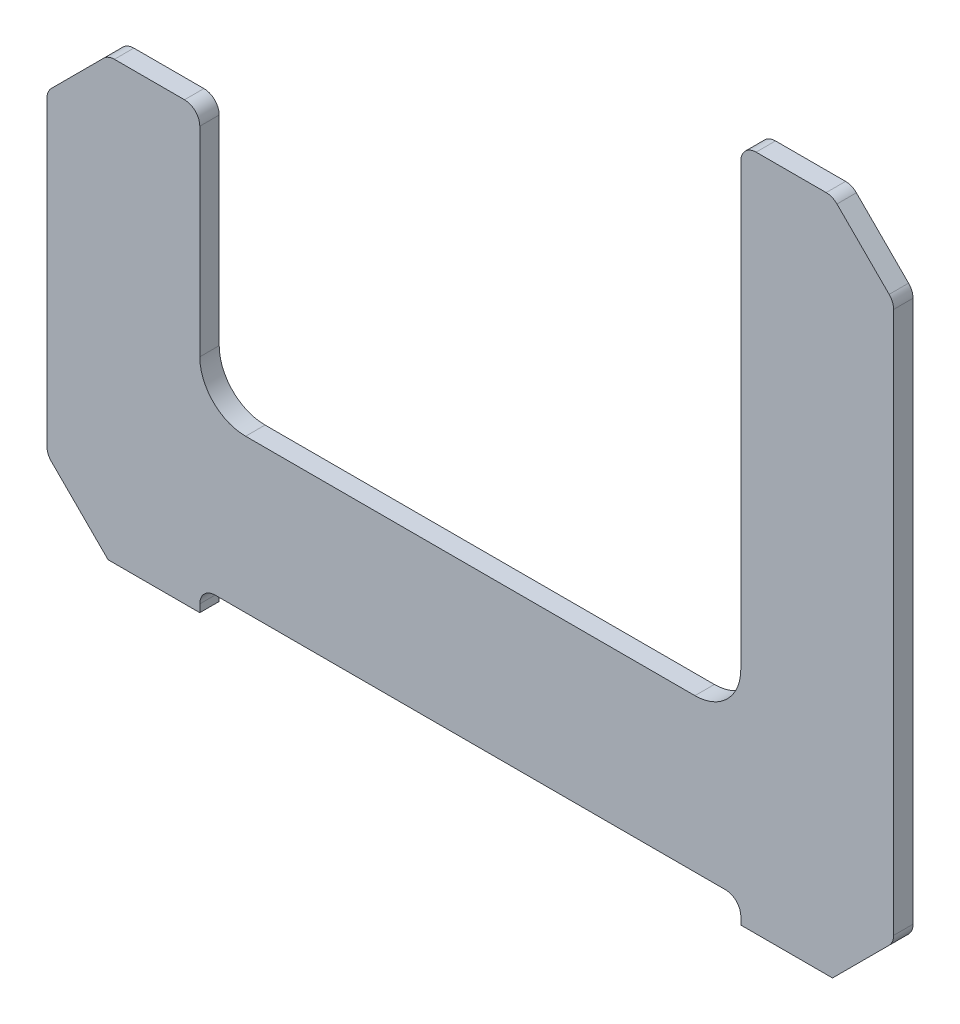
SolidWorks part; units mm, degrees
material "Cedar"
ref_plane "Front Plane" through (0, 0, 0) normal (0, 0, 1) x (1, 0, 0)
ref_plane "Top Plane" through (0, 0, 0) normal (0, 1, 0) x (1, 0, 0)
ref_plane "Right Plane" through (0, 0, 0) normal (1, 0, 0) x (0, 0, -1)
sketch "Sketch2" plane through (0, 0, 0) normal (0, 0, 1) x (1, 0, 0)
  line L0 (-138.5, 85.3385) -> (-88.5, 85.3385)
  line L1 (-88.5, 85.3385) -> (-88.5, 0)
  line L2 (-88.5, 0) -> (88.5, 0)
  line L3 (88.5, 0) -> (88.5, 164)
  line L4 (88.5, 164) -> (138.5, 164)
  line L5 (138.5, 164) -> (138.5, -57.5)
  line L6 (138.5, -57.5) -> (88.5, -57.5)
  line L7 (88.5, -57.5) -> (88.5, -50)
  line L8 (88.5, -50) -> (-88.5, -50)
  line L9 (-88.5, -50) -> (-88.5, -57.5)
  line L10 (-88.5, -57.5) -> (-138.5, -57.5)
  line L11 (-138.5, -57.5) -> (-138.5, 85.3385)
  line L12 (-33.5, 0) -> (-33.5, 124) construction
  point P10 (-33.5, 0)
  point P14 (88.5, 124)
  point P15 (-33.5, 85.3385)
  dimension "D1" = 124
  dimension "D2" = 122
  dimension "D3" = 55
  dimension "D4" = 40
  dimension "D5" = 50
  dimension "D6" = 50
  dimension "D7" = 7.5
extrude "Boss-Extrude1" add sketch "Sketch2" along normal blind 3.175 and the other way blind 3.175
chamfer "Chamfer1" distance 20 angle 45 4 edges at (-138.5, -57.5, 0) (138.5, -57.5, 0) (138.5, 164, 0) (-138.5, 85.3385, 0)
fillet "Fillet1" radius 15 2 edges at (88.5, 0, 0) (-88.5, 0, 0)
fillet "Fillet2" radius 5 10 edges at (138.5, -37.5, 0) (88.5, -50, 0) (-88.5, -50, 0) (-138.5, -37.5, 0) (-138.5, 65.3385, 0) (-118.5, 85.3385, 0) (-88.5, 85.3385, 0) (138.5, 144, 0) (118.5, 164, 0) (88.5, 164, 0)
sketch "Sketch3" plane through (0, 0, 3.175) normal (0, 0, 1) x (1, 0, 0)
  line L0 (-94.6381, 69.9757) -> (-94.6381, 14.7992)
  line L1 (-94.6381, 14.7992) -> (-97.8131, 14.7992)
  line L2 (-97.8131, 14.7992) -> (-97.8131, 69.9757)
  line L3 (-97.8131, 69.9757) -> (-94.6381, 69.9757)
  line L4 (-127.4635, 65.4691) -> (-114.3536, 78.579)
  line L5 (-114.3536, 78.579) -> (-112.1085, 76.3339)
  line L6 (-112.1085, 76.3339) -> (-125.2184, 63.2241)
  line L7 (-125.2184, 63.2241) -> (-127.4635, 65.4691)
  line L8 (-129.3392, 54.7846) -> (-126.1642, 54.7846)
  line L9 (-126.1642, 54.7846) -> (-126.1642, -28.3138)
  line L10 (-126.1642, -28.3138) -> (-129.3392, -28.3138)
  line L11 (-129.3392, -28.3138) -> (-129.3392, 54.7846)
  line L12 (-127.4635, -37.1329) -> (-125.2184, -34.8879)
  line L13 (-125.2184, -34.8879) -> (-110.9382, -49.1681)
  line L14 (-110.9382, -49.1681) -> (-113.1832, -51.4132)
  line L15 (-113.1832, -51.4132) -> (-127.4635, -37.1329)
  line L16 (-67.7784, -44.3183) -> (-67.7784, -41.1433)
  line L17 (-67.7784, -41.1433) -> (53.0181, -41.1433)
  line L18 (53.0181, -41.1433) -> (53.0181, -44.3183)
  line L19 (53.0181, -44.3183) -> (-67.7784, -44.3183)
  line L20 (114.9313, -49.5303) -> (117.1763, -51.7753)
  line L21 (117.1763, -51.7753) -> (131.7883, -37.1634)
  line L22 (131.7883, -37.1634) -> (129.5432, -34.9183)
  line L23 (129.5432, -34.9183) -> (114.9313, -49.5303)
  line L24 (-67.7784, -4.1746) -> (-67.7784, -7.3496)
  line L25 (-67.7784, -7.3496) -> (63.5847, -7.3496)
  line L26 (63.5847, -7.3496) -> (63.5847, -4.1746)
  line L27 (63.5847, -4.1746) -> (-67.7784, -4.1746)
  line L28 (92.7516, 20.9162) -> (91.2159, 151.9937)
  line L29 (91.2159, 151.9937) -> (94.3909, 151.9937)
  line L30 (94.3909, 151.9937) -> (95.9266, 20.9162)
  line L31 (95.9266, 20.9162) -> (92.7516, 20.9162)
  line L32 (96.8341, 161.8762) -> (96.8341, 158.7012)
  line L33 (96.8341, 158.7012) -> (112.5649, 158.7012)
  line L34 (112.5649, 158.7012) -> (112.5649, 161.8762)
  line L35 (112.5649, 161.8762) -> (96.8341, 161.8762)
  line L37 (117.7781, 156.4535) -> (120.0231, 158.6985)
  line L38 (120.0231, 158.6985) -> (133.8694, 144.8523)
  line L39 (133.8694, 144.8523) -> (131.6243, 142.6072)
  line L40 (131.6243, 142.6072) -> (117.7781, 156.4535)
  line L41 (129.9213, 134.1701) -> (133.0963, 134.1701)
  line L42 (133.0963, 134.1701) -> (133.0963, -24.961)
  line L43 (133.0963, -24.961) -> (129.9213, -24.961)
  line L44 (129.9213, -24.961) -> (129.9213, 134.1701)
  line L45 (118.5, -57.5) -> (137.0355, -38.9645) construction
  line L46 (-137.0355, -38.9645) -> (-118.5, -57.5) construction
  line L47 (-119.9645, 83.874) -> (-137.0355, 66.8029) construction
  line L48 (137.0355, 145.4645) -> (119.9645, 162.5355) construction
  dimension "D1" = 3.175
extrude "Cut-Extrude1" [suppressed] cut sketch "Sketch3" against normal through all
sketch "magnets" plane through (0, 0, 3.175) normal (0, 0, 1) x (1, 0, 0)
  point P0 (94.6751, 158.4052)
  point P1 (114.7572, -50)
  point P2 (131.9288, 140.6094)
  point P3 (131.9288, -32.8111)
  point P4 (0, -44.1618)
  point P5 (-114.0039, -50)
  point P6 (-130.8821, -32.8111)
  point P9 (-130.8821, 62.3605)
  point P10 (-93.5499, 79.7316)
  point P12 (0, -4.7392)
sketch "Sketch4" plane through (0, 0, 3.175) normal (0, 0, 1) x (1, 0, 0)
  line L0 (99.9645, 164) -> (99.9645, 160.825)
  line L1 (116.4289, 164) -> (93.5, 164) construction
  line L2 (99.9645, 160.825) -> (109.9645, 160.825)
  line L3 (109.9645, 160.825) -> (109.9645, 164)
  line L4 (124.9645, 157.5355) -> (122.7194, 155.2905)
  line L5 (137.0355, 145.4645) -> (119.9645, 162.5355) construction
  line L6 (122.7194, 155.2905) -> (129.7905, 148.2194)
  line L7 (129.7905, 148.2194) -> (132.0355, 150.4645)
  line L8 (88.5, 137) -> (91.675, 137)
  line L9 (88.5, 159) -> (88.5, 15) construction
  line L10 (91.675, 137) -> (91.675, 37)
  line L11 (91.675, 37) -> (88.5, 37)
  line L12 (138.5, 103.25) -> (135.325, 103.25)
  line L13 (138.5, -35.4289) -> (138.5, 141.9289) construction
  line L14 (135.325, 103.25) -> (135.325, 3.25)
  line L15 (135.325, 3.25) -> (138.5, 3.25)
  line L16 (-50, 0) -> (-50, -3.175)
  line L17 (73.5, 0) -> (-73.5, 0) construction
  line L18 (-50, -3.175) -> (50, -3.175)
  line L19 (50, -3.175) -> (50, 0)
  line L20 (-50, -50) -> (-50, -46.825)
  line L21 (-83.5, -50) -> (83.5, -50) construction
  line L22 (-50, -46.825) -> (50, -46.825)
  line L23 (50, -46.825) -> (50, -50)
  line L24 (-135.325, -6.0808) -> (-138.5, -6.0808)
  line L25 (-138.5, 63.2674) -> (-138.5, -35.4289) construction
  line L26 (-135.325, 33.9192) -> (-135.325, -6.0808)
  line L27 (-135.325, 33.9192) -> (-138.5, 33.9192)
  line L28 (-132.0355, 71.8029) -> (-129.7905, 69.5579)
  line L29 (-119.9645, 83.874) -> (-137.0355, 66.8029) construction
  line L30 (-129.7905, 69.5579) -> (-122.7194, 76.6289)
  line L31 (-122.7194, 76.6289) -> (-124.9645, 78.874)
  line L32 (-109.9645, 85.3385) -> (-109.9645, 82.1635)
  line L33 (-93.5, 85.3385) -> (-116.4289, 85.3385) construction
  line L35 (-109.9645, 82.1635) -> (-99.9645, 82.1635)
  line L36 (-88.5, 67.6692) -> (-91.675, 67.6692)
  line L37 (-88.5, 15) -> (-88.5, 80.3385) construction
  line L38 (-91.675, 67.6692) -> (-91.675, 27.6692)
  line L39 (-91.675, 27.6692) -> (-88.5, 27.6692)
  line L40 (-107.375, -57.5) -> (-107.375, -54.325)
  line L41 (-118.5, -57.5) -> (-88.5, -57.5) construction
  line L42 (-107.375, -54.325) -> (-97.375, -54.325)
  line L43 (-97.375, -54.325) -> (-97.375, -57.5)
  line L44 (97.375, -57.5) -> (97.375, -54.325)
  line L45 (88.5, -57.5) -> (118.5, -57.5) construction
  line L46 (97.375, -54.325) -> (107.375, -54.325)
  line L47 (107.375, -54.325) -> (107.375, -57.5)
  line L48 (-132.0988, -43.9012) -> (-129.8537, -41.6561)
  line L49 (-137.0355, -38.9645) -> (-118.5, -57.5) construction
  line L50 (-129.8537, -41.6561) -> (-122.7827, -48.7272)
  line L51 (-122.7827, -48.7272) -> (-125.0277, -50.9723)
  line L52 (125.0277, -50.9723) -> (122.7827, -48.7272)
  line L53 (118.5, -57.5) -> (137.0355, -38.9645) construction
  line L54 (122.7827, -48.7272) -> (129.8537, -41.6561)
  line L55 (129.8537, -41.6561) -> (132.0988, -43.9012)
  line L56 (-128.5633, -47.4367) -> (-126.3182, -45.1917) construction
  line L57 (-102.375, -57.5) -> (-102.375, -54.325)
  line L58 (102.375, -57.5) -> (102.375, -54.325)
  line L59 (-128.5, 75.3385) -> (-126.2549, 73.0934) construction
  line L60 (-104.9645, 82.1635) -> (-104.9645, 85.3385) construction
  line L61 (126.2549, 151.7549) -> (128.5, 154) construction
  line L62 (126.3182, -45.1917) -> (128.5633, -47.4367) construction
  line L63 (88.5, -57.5) -> (116.25, -57.5) construction
  line L64 (120.091, -55.909) -> (137.0355, -38.9645) construction
  line L65 (120.091, -55.909) -> (118.5, -57.5) construction
  line L66 (118.5, -57.5) -> (116.25, -57.5) construction
  line L67 (-88.5, -57.5) -> (-116.25, -57.5) construction
  line L68 (-116.25, -57.5) -> (-118.5, -57.5) construction
  line L69 (-118.5, -57.5) -> (-120.091, -55.909) construction
  line L70 (-120.091, -55.909) -> (-137.0355, -38.9645) construction
  line L71 (-99.9645, 82.1635) -> (-99.9645, 85.3385)
  point P95 (0, -46.825)
  point P97 (0, -50)
  point P99 (0, -3.175)
  point P101 (135.325, 53.25)
  point P103 (138.5, 53.25)
  point P104 (91.675, 87)
  point P105 (88.5, 87)
  point P106 (104.9645, 160.825)
  point P107 (104.9645, 164)
  point P108 (128.5, 154)
  point P109 (126.2549, 151.7549)
  point P112 (-135.325, 13.9192)
  point P113 (-138.5, 13.9192)
  point P114 (-91.675, 47.6692)
  point P115 (-88.5, 47.6692)
  point P116 (126.3182, -45.1917)
  point P117 (127.7678, -48.2322)
  line M1 (118.5, -57.5) -> (137.0355, -38.9645)
  line M3 (138.5, -35.4289) -> (138.5, 141.9289)
  line M5 (137.0355, 145.4645) -> (119.9645, 162.5355)
  line M7 (116.4289, 164) -> (93.5, 164)
  line M9 (88.5, 159) -> (88.5, 15)
  line M11 (73.5, 0) -> (-73.5, 0)
  line M13 (-88.5, 15) -> (-88.5, 80.3385)
  line M15 (-93.5, 85.3385) -> (-116.4289, 85.3385)
  line M17 (-119.9645, 83.874) -> (-137.0355, 66.8029)
  line M19 (-138.5, 63.2674) -> (-138.5, -35.4289)
  line M21 (-137.0355, -38.9645) -> (-118.5, -57.5)
  line M22 (-118.5, -57.5) -> (-88.5, -57.5)
  line M25 (-83.5, -50) -> (83.5, -50)
  line M28 (88.5, -57.5) -> (118.5, -57.5)
  dimension "D1" = 3.175
  dimension "D5" = 100
  dimension "D6" = 100
  dimension "D7" = 100
  dimension "D8" = 100
  dimension "D4" = 10
  dimension "D2" = 10
  dimension "D10" = 2.25
  dimension "D3" = 2.25
  dimension "D11" = 10
  dimension "D13" = 3.175
  dimension "D12" = 10
  dimension "D14" = 10
  dimension "D15" = 10
  dimension "D16" = 10
  dimension "D17" = 10
  dimension "D18" = 40
  dimension "D19" = 3.175
extrude "wall_slots" [suppressed] cut sketch "Sketch4" against normal blind 60 contours L26 L27 L24 M19 | L18 L19 L16 M11 | L23 L22 L20 M25 | L51 L50 L48 M21 | L57 L43 L42 M22 | L57 L42 L40 M22 | L38 L39 L36 M13 | L35 L71 L32 M15 | L30 L31 L28 M17 | L58 L47 L46 M28 | L58 L46 L44 M28 | L55 L54 L52 M1 | L14 L15 L12 M3 | L11 L10 L8 M9 | L2 L3 L0 M7 | L6 L7 L4 M5
sketch "wall_measure" [suppressed] plane through (0, 0, 3.175) normal (0, 0, 1) x (1, 0, 0)
  line L0 (-116.4289, 85.3385) -> (-116.4289, 82.1635)
  line L1 (-116.4289, 82.1635) -> (-93.5, 82.1635)
  line L2 (-93.5, 82.1635) -> (-93.5, 85.3385)
  line L4 (93.5, 164) -> (93.5, 160.825)
  line L5 (93.5, 160.825) -> (116.4289, 160.825)
  line L6 (116.4289, 160.825) -> (116.4289, 164)
  line L7 (99.9645, 160.825) -> (109.9645, 160.825) construction
  line L8 (119.9645, 162.5355) -> (117.7194, 160.2905)
  line L9 (117.7194, 160.2905) -> (134.7905, 143.2194)
  line L10 (134.7905, 143.2194) -> (137.0355, 145.4645)
  line L11 (137.0355, 145.4645) -> (132.0355, 150.4645) construction
  line L12 (88.5, 159) -> (91.675, 159)
  line L13 (91.675, 159) -> (91.675, 15)
  line L14 (91.675, 15) -> (88.5, 15)
  line L15 (88.5, 37) -> (88.5, 15) construction
  line L16 (138.5, 141.9289) -> (135.325, 141.9289)
  line L17 (135.325, 141.9289) -> (135.325, -35.4289)
  line L18 (135.325, -35.4289) -> (138.5, -35.4289)
  line L19 (-73.5, 0) -> (-73.5, -3.175)
  line L20 (-73.5, -3.175) -> (73.5, -3.175)
  line L21 (73.5, -3.175) -> (73.5, 0)
  line L22 (-83.5, -50) -> (-83.5, -46.825)
  line L23 (-83.5, -46.825) -> (83.5, -46.825)
  line L24 (83.5, -46.825) -> (83.5, -50)
  line L25 (88.5, -55) -> (116.2868, -55)
  line L26 (116.2868, -55) -> (116.2868, -57.5)
  line L27 (137.0355, -38.9645) -> (134.7905, -36.7194)
  line L28 (134.7905, -36.7194) -> (117.8199, -53.69)
  line L29 (117.8199, -53.69) -> (120.065, -55.935)
  line L30 (118.5, -57.5) -> (125.0277, -50.9723) construction
  line L31 (122.7827, -48.7272) -> (129.8537, -41.6561) construction
  line L32 (116.2868, -57.5) -> (118.5, -57.5) construction
  line L33 (118.5, -57.5) -> (120.065, -55.935) construction
  line L34 (-138.5, 63.2674) -> (-133.5, 63.2674)
  line L35 (-133.5, 63.2674) -> (-133.5, -35.4289)
  line L36 (-133.5, -35.4289) -> (-138.5, -35.4289)
  line L37 (-88.5, 80.3385) -> (-91.675, 80.3385)
  line L38 (-91.675, 80.3385) -> (-91.675, 15)
  line L39 (-91.675, 15) -> (-88.5, 15)
  line L40 (-50, -46.825) -> (50, -46.825) construction
  line L41 (-50, -3.175) -> (50, -3.175) construction
  line L42 (135.325, 103.25) -> (135.325, 3.25) construction
  line L43 (91.675, 137) -> (91.675, 37) construction
  line L44 (122.7194, 155.2905) -> (129.7905, 148.2194) construction
  line L45 (-91.675, 67.6692) -> (-91.675, 27.6692) construction
  line L47 (-109.9645, 82.1635) -> (-99.9645, 82.1635) construction
  arc A0 (73.5, 0) -> (88.5, 15) centre (73.5, 15) ccw construction
  arc A1 (-88.5, 15) -> (-73.5, 0) centre (-73.5, 15) ccw construction
  dimension "D1" = 22.9289
  dimension "D2" = 22.9289
  dimension "D3" = 24.1421
  dimension "D4" = 144
  dimension "D5" = 177.3579
  dimension "D6" = 147
  dimension "D7" = 167
  dimension "D8" = 24
  dimension "D9" = 2.2132
  dimension "D10" = 27.7868
  dimension "D11" = 98.6963
  dimension "D12" = 65.3385
sketch "perimeter" plane through (0, 0, 3.175) normal (0, 0, 1) x (1, 0, 0)
  line L16 (118.5, -57.5) -> (137.0355, -38.9645)
  line L17 (138.5, -35.4289) -> (138.5, 141.9289)
  line L18 (137.0355, 145.4645) -> (119.9645, 162.5355)
  line L19 (116.4289, 164) -> (93.5, 164)
  line L20 (88.5, 159) -> (88.5, 15)
  line L21 (73.5, 0) -> (-73.5, 0)
  line L22 (-88.5, 15) -> (-88.5, 80.3385)
  line L23 (-93.5, 85.3385) -> (-116.4289, 85.3385)
  line L24 (-119.9645, 83.874) -> (-137.0355, 66.8029)
  line L25 (-138.5, 63.2674) -> (-138.5, -35.4289)
  line L26 (-137.0355, -38.9645) -> (-118.5, -57.5)
  line L27 (-118.5, -57.5) -> (-88.5, -57.5)
  line L28 (-88.5, -57.5) -> (-88.5, -55)
  line L29 (-83.5, -50) -> (83.5, -50)
  line L30 (88.5, -55) -> (88.5, -57.5)
  line L31 (88.5, -57.5) -> (118.5, -57.5)
  line L32 (118.5, -57.5) -> (137.0355, -38.9645)
  line L33 (138.5, -35.4289) -> (138.5, 141.9289)
  line L34 (137.0355, 145.4645) -> (119.9645, 162.5355)
  line L35 (116.4289, 164) -> (93.5, 164)
  line L36 (88.5, 159) -> (88.5, 15)
  line L37 (73.5, 0) -> (-73.5, 0)
  line L38 (-88.5, 15) -> (-88.5, 80.3385)
  line L39 (-93.5, 85.3385) -> (-116.4289, 85.3385)
  line L40 (-119.9645, 83.874) -> (-137.0355, 66.8029)
  line L41 (-138.5, 63.2674) -> (-138.5, -35.4289)
  line L42 (-137.0355, -38.9645) -> (-118.5, -57.5)
  line L43 (-118.5, -57.5) -> (-88.5, -57.5)
  line L44 (-88.5, -57.5) -> (-88.5, -55)
  line L45 (-83.5, -50) -> (83.5, -50)
  line L46 (88.5, -55) -> (88.5, -57.5)
  line L47 (88.5, -57.5) -> (118.5, -57.5)
  arc A12 (137.0355, -38.9645) -> (138.5, -35.4289) centre (133.5, -35.4289) ccw
  arc A13 (138.5, 141.9289) -> (137.0355, 145.4645) centre (133.5, 141.9289) ccw
  arc A14 (119.9645, 162.5355) -> (116.4289, 164) centre (116.4289, 159) ccw
  arc A15 (93.5, 164) -> (88.5, 159) centre (93.5, 159) ccw
  arc A16 (73.5, 0) -> (88.5, 15) centre (73.5, 15) ccw
  arc A17 (-88.5, 15) -> (-73.5, 0) centre (-73.5, 15) ccw
  arc A18 (-88.5, 80.3385) -> (-93.5, 85.3385) centre (-93.5, 80.3385) ccw
  arc A19 (-116.4289, 85.3385) -> (-119.9645, 83.874) centre (-116.4289, 80.3385) ccw
  arc A20 (-137.0355, 66.8029) -> (-138.5, 63.2674) centre (-133.5, 63.2674) ccw
  arc A21 (-138.5, -35.4289) -> (-137.0355, -38.9645) centre (-133.5, -35.4289) ccw
  arc A22 (-83.5, -50) -> (-88.5, -55) centre (-83.5, -55) ccw
  arc A23 (88.5, -55) -> (83.5, -50) centre (83.5, -55) ccw
  arc A24 (137.0355, -38.9645) -> (138.5, -35.4289) centre (133.5, -35.4289) ccw
  arc A25 (138.5, 141.9289) -> (137.0355, 145.4645) centre (133.5, 141.9289) ccw
  arc A26 (119.9645, 162.5355) -> (116.4289, 164) centre (116.4289, 159) ccw
  arc A27 (93.5, 164) -> (88.5, 159) centre (93.5, 159) ccw
  arc A28 (73.5, 0) -> (88.5, 15) centre (73.5, 15) ccw
  arc A29 (-88.5, 15) -> (-73.5, 0) centre (-73.5, 15) ccw
  arc A30 (-88.5, 80.3385) -> (-93.5, 85.3385) centre (-93.5, 80.3385) ccw
  arc A31 (-116.4289, 85.3385) -> (-119.9645, 83.874) centre (-116.4289, 80.3385) ccw
  arc A32 (-137.0355, 66.8029) -> (-138.5, 63.2674) centre (-133.5, 63.2674) ccw
  arc A33 (-138.5, -35.4289) -> (-137.0355, -38.9645) centre (-133.5, -35.4289) ccw
  arc A34 (-83.5, -50) -> (-88.5, -55) centre (-83.5, -55) ccw
  arc A35 (88.5, -55) -> (83.5, -50) centre (83.5, -55) ccw
  dimension "D1" = 0
equation "\"dX\"= 122mm"
equation "\"dY\"= 124mm"
equation "\"hmotor\"= 50mm"
equation "\"D1@Sketch2\"=\"dY\""
equation "\"D2@Sketch2\"=\"dX\""
equation "\"D5@Sketch2\"=\"hmotor\""
equation "\"D6@Sketch2\"=\"hmotor\""
equation "\"t_wood\"= 0.25in"
equation "\"D1@Boss-Extrude1\"=\"t_wood\"/2"
equation "\"D2@Boss-Extrude1\"=\"t_wood\"/2"
equation "\"D1@Sketch3\"=\"t_wood\"/2"
equation "\"D1@Sketch4\"=\"t_wood\"/2"
equation "\"D13@Sketch4\"=\"t_wood\"/2"
equation "\"D19@Sketch4\"=\"t_wood\"/2"
